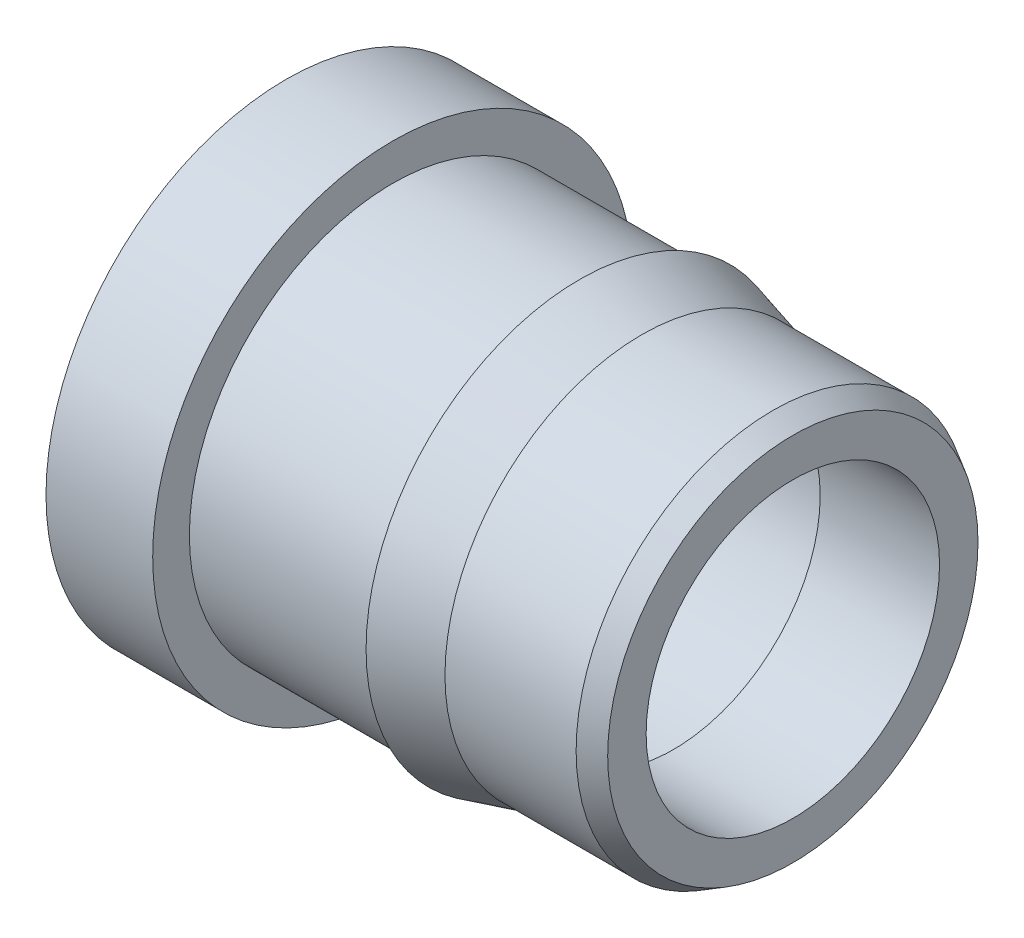
SolidWorks part; units mm, degrees
material "Brass Alloy 385"
ref_plane "Front Plane" through (0, 0, 0) normal (0, 0, 1) x (1, 0, 0)
ref_plane "Top Plane" through (0, 0, 0) normal (0, 1, 0) x (1, 0, 0)
ref_plane "Right Plane" through (0, 0, 0) normal (1, 0, 0) x (0, 0, -1)
sketch "Sketch1" plane through (0, 0, 0) normal (0, 0, 1) x (1, 0, 0)
  line L0 (0, 0) -> (0, 0.9144)
  line L1 (0, 0.9144) -> (0.4064, 0.9144)
  line L2 (0.4064, 0.9144) -> (0.4064, 0.7747)
  line L3 (0.4064, 0.7747) -> (1.1176, 0.7747)
  line L4 (1.1176, 0.7747) -> (1.1176, 0.8128)
  line L5 (1.1176, 0.8128) -> (1.3546, 0.7493)
  line L6 (1.3546, 0.7493) -> (1.8542, 0.7493)
  line L7 (1.8542, 0.7493) -> (1.9304, 0.7053)
  line L8 (1.9304, 0.7053) -> (1.9304, 0)
  line L9 (0, 0) -> (1.9304, 0)
  line L10 (0, 0) -> (1.9304, 0) construction
revolve "RevolutionAngle1" add sketch "Sketch1" angle 360 about L10
hole_wizard "Hole1" positions "Sketch3" profile "Sketch2" legacy
sketch "Sketch3" plane through (0, 0, 0) normal (-1, 0, 0) x (0, 0, 1)
  point P0 (0, 0)
sketch "Sketch2" plane through (0, 0, 0) normal (0, 1, 0) x (0, 0, 1)
  line L0 (0, 0) -> (0, 1.8116)
  line L1 (0, 1.8116) -> (0.6477, 1.4224)
  line L2 (0.6477, 1.4224) -> (0.6477, 0)
  line L4 (0.6477, 0) -> (0, 0)
  line L6 (0, 1.8116) -> (-0.6477, 1.4224) construction
  line L7 (0, -4.2442) -> (0, 117.3081) construction
  dimension "A1" = 1.2954
  dimension "N" = 1.4224
  dimension "Drill Angle" = 118
hole_wizard "Hole2" positions "3DSketch1" profile "Sketch4" legacy end condition through all
sketch3d "3DSketch1"
  line L0 (1.8542, 0, 0) -> (1.9304, 0, 0) construction
  point P0 (1.9304, 0, 0)
sketch "Sketch4" plane through (1.9304, 0, 0) normal (0, 1, 0) x (0, 0, -1)
  line L0 (0, 0) -> (0, 2.2662)
  line L1 (0, 2.2662) -> (0.5588, 1.9304)
  line L2 (0.5588, 1.9304) -> (0.5588, 0)
  line L4 (0.5588, 0) -> (0, 0)
  line L6 (0, 2.2662) -> (-0.5588, 1.9304) construction
  line L7 (0, -4.2442) -> (0, 117.3081) construction
  dimension "A2" = 1.1176
  dimension "Depth" = 1.9304
  dimension "Drill Angle" = 118
